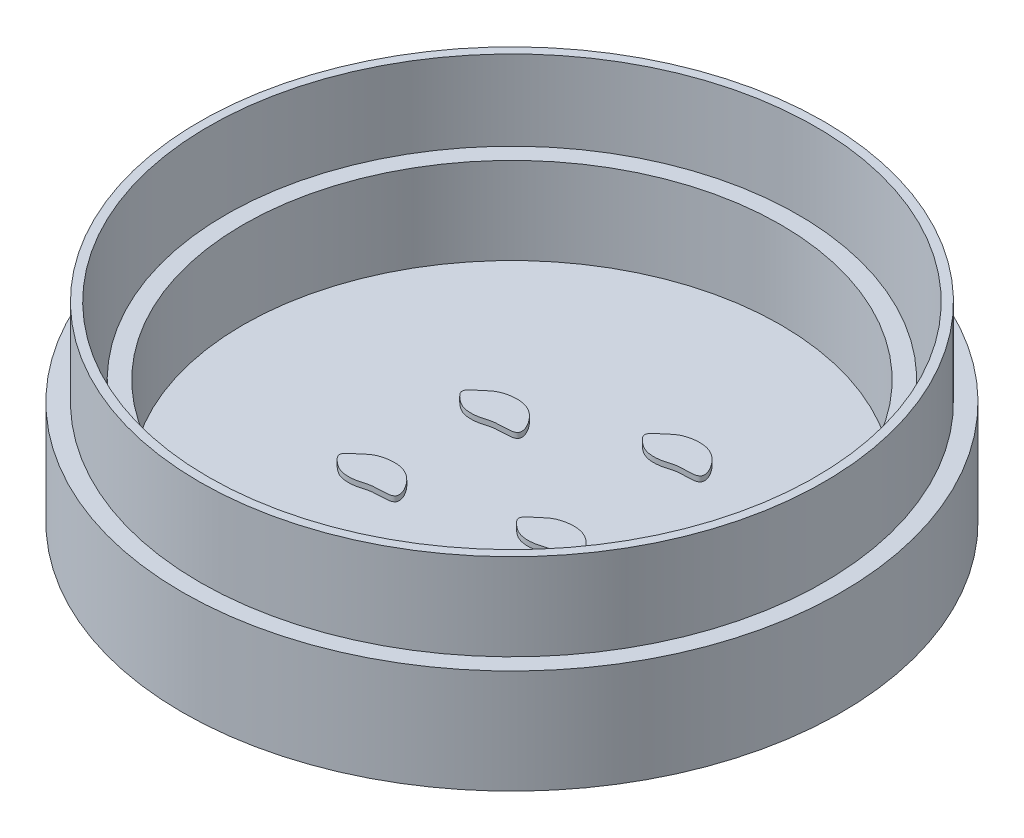
SolidWorks part; units mm, degrees
ref_plane "Front Plane" through (0, 0, 0) normal (0, 0, 1) x (1, 0, 0)
ref_plane "Top Plane" through (0, 0, 0) normal (0, 1, 0) x (1, 0, 0)
ref_plane "Right Plane" through (0, 0, 0) normal (1, 0, 0) x (0, 0, -1)
sketch "Sketch1" plane through (0, 0, 0) normal (0, 1, 0) x (1, 0, 0)
  circle A0 centre (0, 0) radius 19
  dimension "D1" = 38
extrude "Boss-Extrude1" add sketch "Sketch1" along normal blind 1
sketch "Sketch2" plane through (0, 1, 0) normal (0, 1, 0) x (1, 0, 0)
  circle A0 centre (0, 0) radius 19
  circle A1 centre (0, 0) radius 17.5
  dimension "D1" = 1.5
  dimension "D2" = 38
extrude "Boss-Extrude2" add sketch "Sketch2" along normal blind 5
sketch "Sketch3" plane through (0, 6, 0) normal (0, 1, 0) x (1, 0, 0)
  circle A0 centre (0, 0) radius 17.5
  circle A1 centre (0, 0) radius 18
  dimension "D1" = 35
  dimension "D2" = 0.5
extrude "Boss-Extrude3" add sketch "Sketch3" along normal blind 5
ref_plane "Plane1" through (0, 2, 0) normal (0, 1, 0) x (1, 0, 0)
sketch "Sketch4" plane through (0, 2, 0) normal (0, 1, 0) x (1, 0, 0)
  circle A0 centre (0, 0) radius 16.5
  dimension "D1" = 33
extrude "membrane" add sketch "Sketch4" along normal blind 0.1 separate body
sketch "Sketch5" plane through (0, 2.1, 0) normal (0, 1, 0) x (1, 0, 0)
  circle A0 centre (0, 0) radius 16.5
  circle A1 centre (0, 0) radius 15.5
  dimension "D1" = 1
  dimension "D2" = 33
extrude "Boss-Extrude5" add sketch "Sketch5" along normal blind 5 separate body
sketch "Sketch6" plane through (0, 2.1, 0) normal (0, 1, 0) x (1, 0, 0)
  spline S0 degree 3 poles (-5.7934, 2.7704) (-5.1014, 3.2121) (-4.5925, 3.7369) (-3.5763, 3.9958) (-2.414, 3.7011) (-1.3945, 1.9411) (-3.0019, 2.1877) (-3.8486, 1.8313) (-4.7051, 1.8404) (-5.2502, 2.2337) (-5.7934, 2.7704) (-5.1014, 3.2121) (-4.5925, 3.7369) knots -0.207528 -0.144238 -0.088559 0 0.051935 0.170654 0.317123 0.463291 0.601985 0.676443 0.792472 0.855762 0.911441 1 1.051935 1.170654 1.317123 only from (-5.0595, 3.2819) to (-5.0595, 3.2819)
  spline S1 degree 3 poles (2.1851, -1.9363) (2.8772, -1.4946) (3.3861, -0.9698) (4.4023, -0.7109) (5.5645, -1.0056) (6.584, -2.7656) (4.9766, -2.519) (4.13, -2.8754) (3.2735, -2.8663) (2.7283, -2.473) (2.1851, -1.9363) (2.8772, -1.4946) (3.3861, -0.9698) knots -0.207528 -0.144238 -0.088559 0 0.051935 0.170654 0.317123 0.463291 0.601985 0.676443 0.792472 0.855762 0.911441 1 1.051935 1.170654 1.317123 only from (2.9191, -1.4248) to (2.9191, -1.4248)
  spline S2 degree 3 poles (-5.7934, 2.7704) (-5.1014, 3.2121) (-4.5925, 3.7369) (-3.5763, 3.9958) (-2.414, 3.7011) (-1.3945, 1.9411) (-3.0019, 2.1877) (-3.8486, 1.8313) (-4.7051, 1.8404) (-5.2502, 2.2337) (-5.7934, 2.7704) (-5.1014, 3.2121) (-4.5925, 3.7369) knots -0.207528 -0.144238 -0.088559 0 0.051935 0.170654 0.317123 0.463291 0.601985 0.676443 0.792472 0.855762 0.911441 1 1.051935 1.170654 1.317123 only from (-5.0595, 3.2819) to (-5.0595, 3.2819)
  spline S3 degree 3 poles (1.6416, 5.863) (2.3336, 6.3047) (2.8425, 6.8296) (3.8587, 7.0884) (5.021, 6.7938) (6.0405, 5.0338) (4.4331, 5.2804) (3.5864, 4.9239) (2.7299, 4.933) (2.1848, 5.3263) (1.6416, 5.863) (2.3336, 6.3047) (2.8425, 6.8296) knots -0.207528 -0.144238 -0.088559 0 0.051935 0.170654 0.317123 0.463291 0.601985 0.676443 0.792472 0.855762 0.911441 1 1.051935 1.170654 1.317123 only from (2.3755, 6.3745) to (2.3755, 6.3745)
  spline S4 degree 3 poles (-6.163, -3.9318) (-5.4709, -3.4901) (-4.962, -2.9653) (-3.9458, -2.7064) (-2.7836, -3.0011) (-1.7641, -4.7611) (-3.3715, -4.5145) (-4.2181, -4.8709) (-5.0746, -4.8618) (-5.6198, -4.4685) (-6.163, -3.9318) (-5.4709, -3.4901) (-4.962, -2.9653) knots -0.207528 -0.144238 -0.088559 0 0.051935 0.170654 0.317123 0.463291 0.601985 0.676443 0.792472 0.855762 0.911441 1 1.051935 1.170654 1.317123 only from (-5.429, -3.4203) to (-5.429, -3.4203)
extrude "slices" add sketch "Sketch6" along normal blind 0.3 separate body contours S4 | S0 | S3 | S1
sketch "Sketch7" plane through (0, 1, 0) normal (0, 1, 0) x (1, 0, 0)
  circle A0 centre (0, 0) radius 17.25
  dimension "D1" = 34.5
extrude "Boss-Extrude7" add sketch "Sketch7" along normal blind 1 separate body
